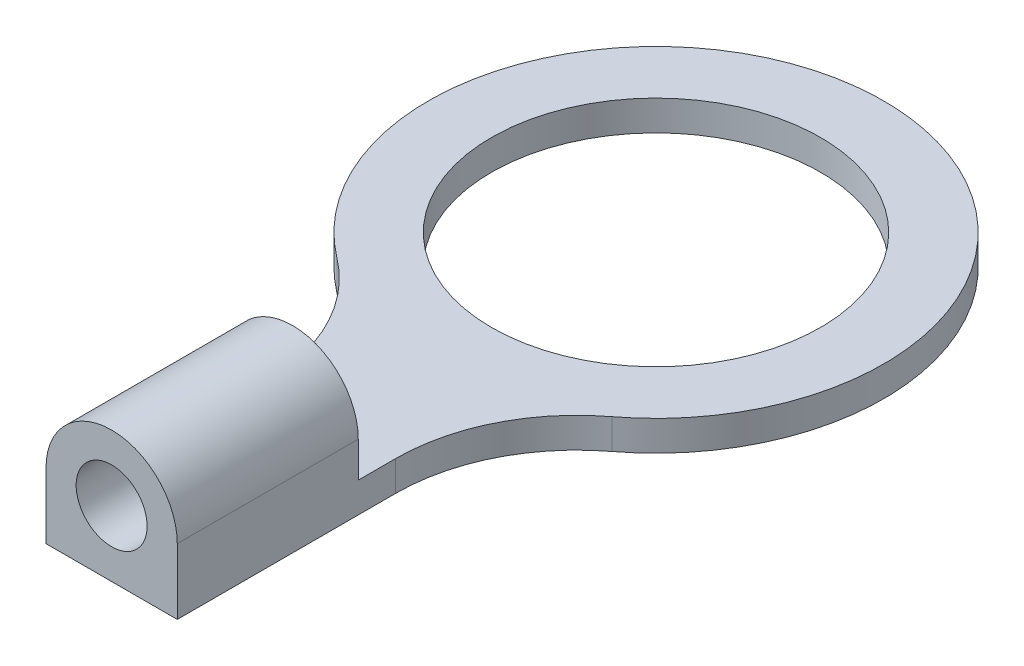
SolidWorks part; units mm, degrees
ref_plane "Front Plane" through (0, 0, 0) normal (0, 0, 1) x (1, 0, 0)
ref_plane "Top Plane" through (0, 0, 0) normal (0, 1, 0) x (1, 0, 0)
ref_plane "Right Plane" through (0, 0, 0) normal (1, 0, 0) x (0, 0, -1)
sketch "Sketch1" plane through (0, 0, 0) normal (0, 1, 0) x (1, 0, 0)
  line L0 (0, 5.9944) -> (0, -14.3256) construction
  line L1 (-1.7272, -14.3256) -> (1.7272, -14.3256)
  line L2 (1.7272, -14.3256) -> (1.7272, -8.5787)
  line L3 (-1.7272, -14.3256) -> (-1.7272, -8.5787)
  circle A0 centre (0, 0) radius 4.3307
  arc A1 (3.6165, -4.7806) -> (-3.6165, -4.7806) centre (0, 0) ccw
  arc A2 (1.7272, -8.5787) -> (3.6165, -4.7806) centre (6.4897, -8.5787) cw
  arc A3 (-1.7272, -8.5787) -> (-3.6165, -4.7806) centre (-6.4897, -8.5787) ccw
  point P8 (0, -14.3256)
  dimension "D1" = 8.6614
  dimension "D2" = 11.9888
  dimension "D6" = 4.7625
  dimension "D3" = 20.32
  dimension "D4" = 3.4544
extrude "Boss-Extrude1" add sketch "Sketch1" along normal blind 0.7937
sketch "Sketch2" plane through (0, 0, 14.3256) normal (0, 0, 1) x (1, 0, 0)
  line L0 (1.7272, 0.7937) -> (1.7272, 0) construction
  line L1 (-1.7272, 0.7937) -> (-1.7272, 0) construction
  line L2 (-1.7272, 0) -> (-1.7272, 1.7272)
  line L3 (1.7272, 1.7272) -> (1.7272, 0)
  line L4 (1.7272, 0) -> (-1.7272, 0)
  line L5 (-1.7272, 0.7937) -> (1.7272, 0.7937) construction
  arc A0 (1.7272, 1.7272) -> (-1.7272, 1.7272) centre (0, 1.7272) ccw
  circle A1 centre (0, 1.7272) radius 0.9334
extrude "Boss-Extrude2" add sketch "Sketch2" against normal blind 4.7625
sketch3d "3DSketch1"
  line L0 (0, 1.7272, 14.3256) -> (0, 1.7272, 9.5631) construction
  circle A0 centre (0, 1.7272, 14.3256) radius 0.9334 construction
  circle A1 centre (0, 1.7272, 9.5631) radius 0.9334 construction
  point P4 (0, 1.7272, 15.259)
  point P5 (0, 0, 0)
  point P6 (0, 0, 0)
  point P9 (0, 1.7272, 10.4966)
  point P10 (0, 0, 0)
